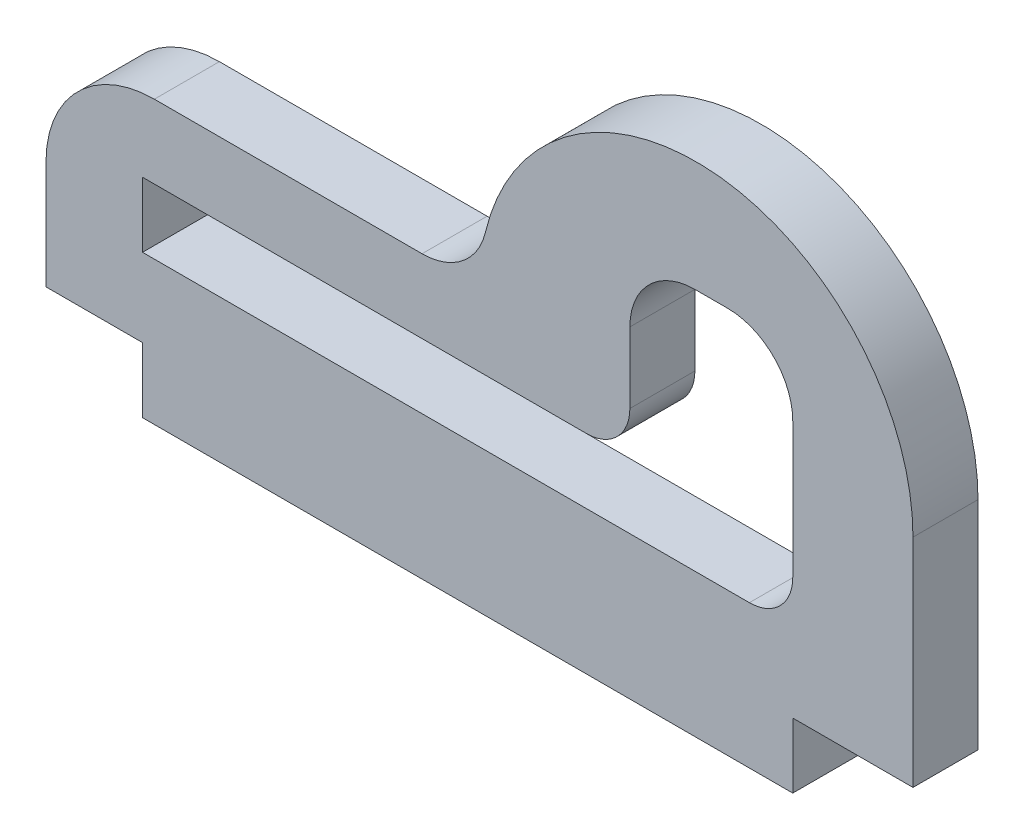
SolidWorks part; units mm, degrees
ref_plane "Alzado" through (0, 0, 0) normal (0, 0, 1) x (1, 0, 0)
ref_plane "Planta" through (0, 0, 0) normal (0, 1, 0) x (1, 0, 0)
ref_plane "Vista lateral" through (0, 0, 0) normal (1, 0, 0) x (0, 0, -1)
sketch "Croquis1" plane through (0, 0, 0) normal (0, 0, 1) x (1, 0, 0)
  line L0 (-2.6491, 0) -> (-15, 0)
  line L1 (-20, -5) -> (-20, -10)
  line L2 (-20, -10) -> (-15.5468, -10)
  line L3 (20, -10) -> (20, 0)
  line L5 (-15.5468, -6.3913) -> (12.4532, -6.3913)
  line L6 (-15.5468, -6.3913) -> (-15.5468, -3.3913)
  line L7 (-15.5468, -3.3913) -> (4.9381, -3.3913)
  line L8 (14.4532, -4.3913) -> (14.4532, -3.3913)
  line L10 (-15.5468, -10) -> (-15.5468, -13)
  line L11 (14.4532, -3.3913) -> (14.4532, 1.8696)
  line L12 (6.9381, -1.3913) -> (6.9381, 1.8696)
  line L13 (11.4532, 4.8696) -> (9.9381, 4.8696)
  line L14 (14.4532, -10) -> (14.4532, -13)
  line L15 (-15.5468, -13) -> (14.4532, -13)
  line L16 (14.4532, -10) -> (20, -10)
  arc A0 (20, 0) -> (0.2699, 2.3077) centre (10, 0) ccw
  arc A1 (-2.6491, 0) -> (0.2699, 2.3077) centre (-2.6491, 3) ccw
  arc A2 (14.4532, 1.8696) -> (11.4532, 4.8696) centre (11.4532, 1.8696) ccw
  arc A3 (6.9381, 1.8696) -> (9.9381, 4.8696) centre (9.9381, 1.8696) cw
  arc A4 (12.4532, -6.3913) -> (14.4532, -4.3913) centre (12.4532, -4.3913) ccw
  arc A5 (4.9381, -3.3913) -> (6.9381, -1.3913) centre (4.9381, -1.3913) ccw
  arc A6 (-15, 0) -> (-20, -5) centre (-15, -5) ccw
  point P7 (-0.5468, -4.8913)
  point P12 (0, 0)
  point P22 (0, 0)
  point P29 (14.4532, -6.3913)
  point P34 (-20, 0)
  dimension "D8" = 3
  dimension "D9" = 2
  dimension "D10" = 5
  dimension "D1" = 40
  dimension "D2" = 10
  dimension "D3" = 20
  dimension "D4" = 10
  dimension "D5" = 3
  dimension "D6" = 30
  dimension "D7" = 3
extrude "Saliente-Extruir1" add sketch "Croquis1" along normal blind 3
